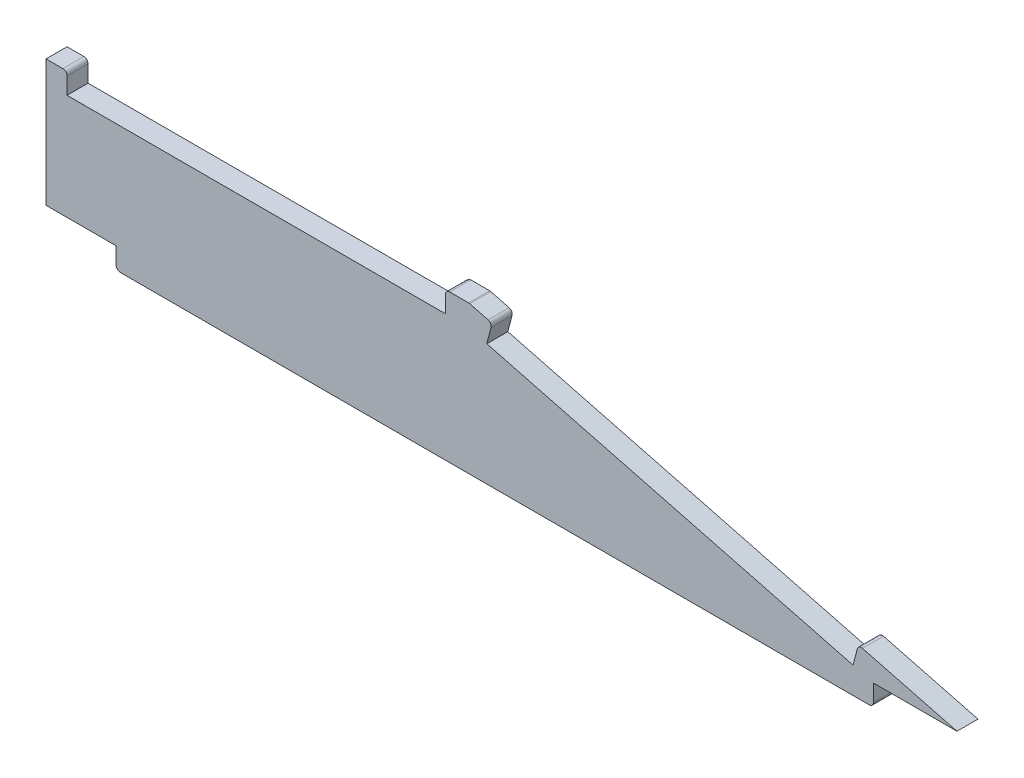
SolidWorks part; units mm, degrees
ref_plane "Front" through (0, 0, 0) normal (0, 0, 1) x (1, 0, 0)
ref_plane "Top" through (0, 0, 0) normal (0, 1, 0) x (1, 0, 0)
ref_plane "Right" through (0, 0, 0) normal (1, 0, 0) x (0, 0, -1)
sketch "Sketch1" plane through (0, 0, 0) normal (0, 0, 1) x (1, 0, 0)
  line L0 (226.1881, 5) -> (227.4461, 9.8391) construction
  line L1 (29.4052, 5) -> (46.0881, 5)
  line L5 (227.4461, 9.8391) -> (222.607, 11.0972) construction
  line L6 (130.6632, 35) -> (129.4052, 30.1609) construction
  line L7 (129.4052, 30.1609) -> (226.1881, 5) construction
  line L8 (134.2443, 28.9028) -> (221.349, 6.258)
  line L9 (134.2443, 28.9028) -> (135.5024, 33.742)
  line L10 (221.349, 6.258) -> (222.607, 11.0972)
  line L12 (222.607, 11.0972) -> (246.0602, 5)
  line L14 (129.4052, 30.1609) -> (29.4052, 30.1609) construction
  line L15 (129.4052, 30.1609) -> (129.4052, 35.1609) construction
  line L16 (129.4052, 35.1609) -> (124.4052, 35.1609) construction
  line L17 (29.4052, 30.1609) -> (29.4052, 35.1609) construction
  line L18 (34.4052, 35.1609) -> (34.4052, 30.1609)
  line L19 (124.4052, 35.1609) -> (124.4052, 30.1609)
  line L20 (34.4052, 30.1609) -> (124.4052, 30.1609)
  line L22 (34.4052, 35.1609) -> (29.4052, 35.1609)
  line L23 (29.4052, 35.1609) -> (29.4052, 5)
  line L25 (46.0881, 5) -> (46.0881, 0)
  line L27 (46.0881, 0) -> (226.1881, 0)
  line L28 (34.4052, 35.1609) -> (29.4052, 35.1609) construction
  line L29 (135.5024, 33.742) -> (130.6632, 35) construction
  line L30 (226.1881, 5) -> (246.0602, 5)
  line L31 (135.5024, 33.742) -> (130.0445, 35.1609)
  line L32 (124.4052, 35.1609) -> (130.0445, 35.1609)
  line L33 (226.1881, 5) -> (226.1881, 0)
  dimension "D1" = 5
  dimension "D2" = 100
  dimension "D3" = 30
  dimension "D4" = 5
  dimension "D5" = 5
  dimension "D6" = 5
  dimension "D7" = 100
  dimension "D8" = 5
  dimension "D9" = 5
  dimension "D10" = 5
  dimension "D11" = 5
  dimension "D12" = 180.1
extrude "Boss-Extrude1" add sketch "Sketch1" along normal blind 5
fillet "Fillet1" radius 1 7 edges at (226.1881, 0, 2.5) (46.0881, 0, 2.5) (34.4052, 35.1609, 2.5) (124.4052, 35.1609, 2.5) (130.0445, 35.1609, 2.5) (135.5024, 33.742, 2.5) (222.607, 11.0972, 2.5)
